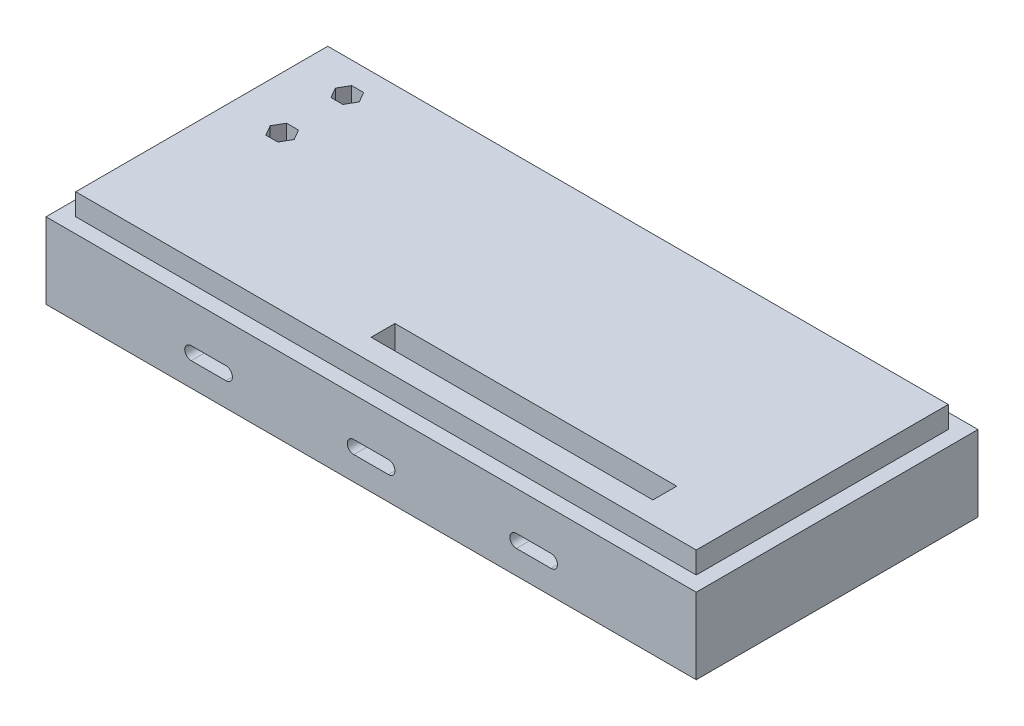
SolidWorks part; units mm, degrees
ref_plane "Front Plane" through (0, 0, 0) normal (0, 0, 1) x (1, 0, 0)
ref_plane "Top Plane" through (0, 0, 0) normal (0, 1, 0) x (1, 0, 0)
ref_plane "Right Plane" through (0, 0, 0) normal (1, 0, 0) x (0, 0, -1)
sketch "Sketch1" plane through (0, 0, 0) normal (0, 1, 0) x (1, 0, 0)
  line L1 (-75, -32.5) -> (75, -32.5)
  line L2 (-75, -32.5) -> (-75, 32.5)
  line L3 (-75, 32.5) -> (75, 32.5)
  line L4 (75, -32.5) -> (75, 32.5)
  line L5 (-75, -32.5) -> (75, 32.5) construction
  line L6 (-75, 32.5) -> (75, -32.5) construction
  point P1 (0, 0)
  dimension "D1" = 150
  dimension "D2" = 65
extrude "Boss-Extrude1" add sketch "Sketch1" along normal blind 17.5
sketch "Sketch2" plane through (0, 0, 32.5) normal (0, 0, 1) x (1, 0, 0)
  line L0 (0, 0) -> (0, 17.5) construction
  line L1 (-75, 17.5) -> (75, 17.5) construction
  line L2 (0, 8.75) -> (-75, 8.75) construction
  line L3 (-75, 17.5) -> (-75, 0) construction
  line L4 (0, 8.75) -> (75, 8.75) construction
  line L5 (-41.5, 7) -> (-33.5, 7) construction
  line L6 (-37.5, 8.75) -> (-37.5, 0) construction
  line L7 (55, 0) -> (-55, 0) construction
  line L8 (75, 17.5) -> (75, 0) construction
  line L9 (37.5, 8.75) -> (37.5, 0) construction
  line L10 (-4, 7) -> (4, 7) construction
  line L11 (-4, 8.5) -> (4, 8.5)
  line L12 (-4, 5.5) -> (4, 5.5)
  line L13 (-41.5, 8.5) -> (-33.5, 8.5)
  line L14 (-41.5, 5.5) -> (-33.5, 5.5)
  line L15 (33.5, 7) -> (41.5, 7) construction
  line L16 (33.5, 8.5) -> (41.5, 8.5)
  line L17 (33.5, 5.5) -> (41.5, 5.5)
  arc A0 (-4, 8.5) -> (-4, 5.5) centre (-4, 7) ccw
  arc A1 (4, 5.5) -> (4, 8.5) centre (4, 7) ccw
  arc A2 (-41.5, 8.5) -> (-41.5, 5.5) centre (-41.5, 7) ccw
  arc A3 (-33.5, 5.5) -> (-33.5, 8.5) centre (-33.5, 7) ccw
  arc A4 (33.5, 8.5) -> (33.5, 5.5) centre (33.5, 7) ccw
  arc A5 (41.5, 5.5) -> (41.5, 8.5) centre (41.5, 7) ccw
  point P20 (0, 7)
  point P29 (-37.5, 7)
  point P37 (37.5, 7)
  dimension "D1" = 8
  dimension "D2" = 3
  dimension "D3" = 5.5
  dimension "D4" = 8
  dimension "D5" = 3
  dimension "D6" = 5.5
  dimension "D7" = 8
  dimension "D8" = 3
  dimension "D9" = 5.5
extrude "Cut-Extrude1" cut sketch "Sketch2" against normal through all
sketch "Sketch3" plane through (0, 17.5, 0) normal (0, 1, 0) x (1, 0, 0)
  line L1 (-71.571, -29.071) -> (71.571, -29.071)
  line L2 (-71.571, -29.071) -> (-71.571, 29.071)
  line L3 (-71.571, 29.071) -> (71.571, 29.071)
  line L4 (71.571, -29.071) -> (71.571, 29.071)
  line L5 (-71.571, -29.071) -> (71.571, 29.071) construction
  line L6 (-71.571, 29.071) -> (71.571, -29.071) construction
  line L7 (-75, 32.5) -> (-75, -32.5) construction
  line L8 (75, 32.5) -> (-75, 32.5) construction
  point P0 (0, 0)
  dimension "D1" = 3.429
  dimension "D2" = 3.429
extrude "Boss-Extrude2" add sketch "Sketch3" along normal blind 5
sketch "Sketch4" plane through (0, 22.5, 0) normal (0, 1, 0) x (1, 0, 0)
  line L0 (-59.571, 21.571) -> (-59.571, 6.551) construction
  line L1 (71.571, 29.071) -> (-71.571, 29.071) construction
  line L2 (-71.571, 29.071) -> (-71.571, -29.071) construction
  line L4 (-60.9509, 23.961) -> (-62.3307, 21.571)
  line L5 (-62.3307, 21.571) -> (-60.9509, 19.181)
  line L6 (-60.9509, 19.181) -> (-58.1911, 19.181)
  line L7 (-58.1911, 19.181) -> (-56.8113, 21.571)
  line L8 (-56.8113, 21.571) -> (-58.1911, 23.961)
  line L9 (-58.1911, 23.961) -> (-60.9509, 23.961)
  line L10 (-60.9509, 8.941) -> (-62.3307, 6.551)
  line L11 (-62.3307, 6.551) -> (-60.9509, 4.161)
  line L12 (-60.9509, 4.161) -> (-58.1911, 4.161)
  line L13 (-58.1911, 4.161) -> (-56.8113, 6.551)
  line L14 (-56.8113, 6.551) -> (-58.1911, 8.941)
  line L15 (-58.1911, 8.941) -> (-60.9509, 8.941)
  circle A2 centre (-59.571, 21.571) radius 2.39 construction
  circle A3 centre (-59.571, 6.551) radius 2.39 construction
  dimension "D3" = 4.78
  dimension "D4" = 4.78
  dimension "D1" = 15.02
  dimension "D2" = 7.5
  dimension "D5" = 12
sketch "Sketch5" plane through (0, 22.5, 0) normal (0, 1, 0) x (1, 0, 0)
  line L1 (-61.591, 4.541) -> (-29.841, 4.541)
  line L2 (-61.591, 4.541) -> (-61.591, 23.591)
  line L3 (-61.591, 23.591) -> (-29.841, 23.591)
  line L4 (-29.841, 4.541) -> (-29.841, 23.591)
  line L5 (-61.591, 4.541) -> (-29.841, 23.591) construction
  line L6 (-61.591, 23.591) -> (-29.841, 4.541) construction
  point P0 (-45.716, 14.066)
  dimension "D3" = 2.02
  dimension "D1" = 19.05
  dimension "D2" = 31.75
  dimension "D4" = 2.02
extrude "Cut-Extrude2" cut sketch "Sketch4" against normal blind 6.5
sketch "Sketch6" plane through (0, 22.5, 0) normal (0, 1, 0) x (1, 0, 0)
  line L0 (-71.571, -29.071) -> (71.571, -29.071) construction
  line L1 (-8.429, -24.071) -> (56.571, -24.071)
  line L2 (-8.429, -24.071) -> (-8.429, -18.571)
  line L3 (-8.429, -18.571) -> (56.571, -18.571)
  line L4 (56.571, -24.071) -> (56.571, -18.571)
  line L5 (-8.429, -24.071) -> (56.571, -18.571) construction
  line L6 (-8.429, -18.571) -> (56.571, -24.071) construction
  line L7 (71.571, -29.071) -> (71.571, 29.071) construction
  point P0 (24.071, -21.321)
  dimension "D1" = 5.5
  dimension "D2" = 65
  dimension "D3" = 5
  dimension "D4" = 15
extrude "Cut-Extrude3" cut sketch "Sketch6" against normal blind 10
